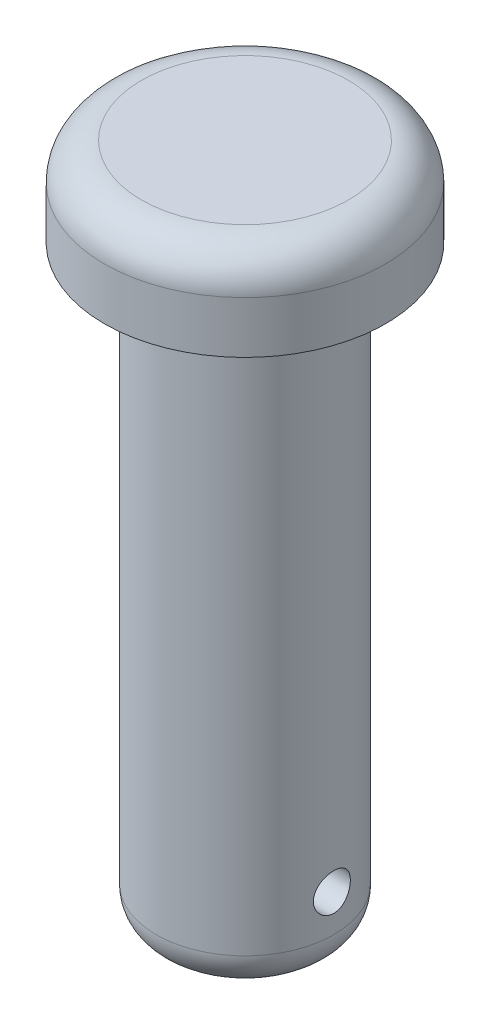
SolidWorks part; units mm, degrees
ref_plane "Front Plane" through (0, 0, 0) normal (0, 0, 1) x (1, 0, 0)
ref_plane "Top Plane" through (0, 0, 0) normal (0, 1, 0) x (1, 0, 0)
ref_plane "Right Plane" through (0, 0, 0) normal (1, 0, 0) x (0, 0, -1)
sketch "Sketch1" plane through (0, 0, 0) normal (0, 0, 1) x (1, 0, 0)
  line L0 (0, 0) -> (0, 87.0769) construction
  line L1 (0, 87.0769) -> (0, -65.5385) construction
  line L2 (0, 52) -> (14, 52)
  line L3 (19, 47) -> (19, 40)
  line L4 (19, 40) -> (12, 40)
  line L5 (12, 40) -> (12, -35)
  line L6 (7, -40) -> (0, -40)
  line L7 (0, 52) -> (0, -40)
  arc A0 (12, -35) -> (7, -40) centre (7, -35) cw
  arc A1 (19, 47) -> (14, 52) centre (14, 47) ccw
  point P13 (12, -40)
  point P16 (19, 52)
  dimension "D5" = 5
  dimension "D6" = 5
  dimension "D1" = 80
  dimension "D2" = 19
  dimension "D3" = 12
  dimension "D4" = 12
  dimension "D7" = 40
revolve "Revolve3" add sketch "Sketch1" angle 360 about L1
sketch "Sketch5" plane through (0, 0, 0) normal (1, 0, 0) x (0, 0, -1)
  line L0 (-7, -40) -> (7, -40) construction
  circle A0 centre (0, -30) radius 2.5
  dimension "D2" = 5
  dimension "D1" = 10
  dimension "D3" = 30
extrude "Cut-Extrude1" cut sketch "Sketch5" against normal mid plane 70
